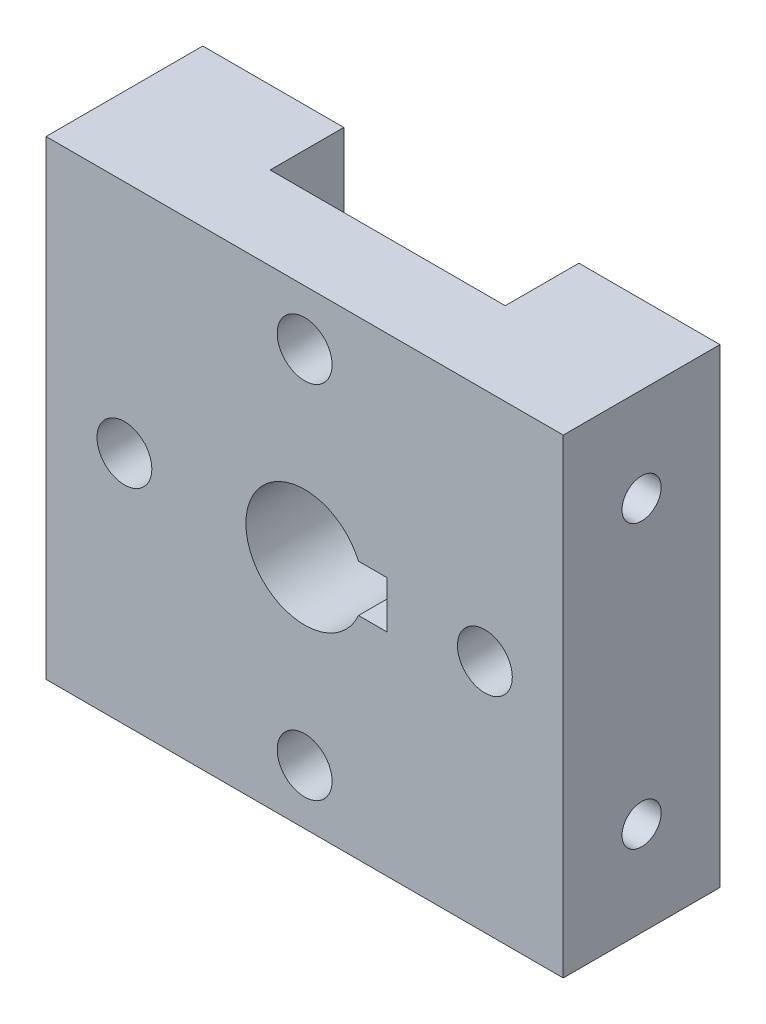
SolidWorks part; units mm, degrees
material "1.0037 (S235JR)"
ref_plane "Front Plane" through (0, 0, 0) normal (0, 0, 1) x (1, 0, 0)
ref_plane "Top Plane" through (0, 0, 0) normal (0, 1, 0) x (1, 0, 0)
ref_plane "Right Plane" through (0, 0, 0) normal (1, 0, 0) x (0, 0, -1)
sketch "Sketch1" plane through (0, 0, 0) normal (0, 0, 1) x (1, 0, 0)
  line L1 (33, 30) -> (-33, 30)
  line L2 (33, 30) -> (33, -30)
  line L3 (33, -30) -> (-33, -30)
  line L4 (-33, 30) -> (-33, -30)
  line L5 (33, 30) -> (-33, -30) construction
  line L6 (33, -30) -> (-33, 30) construction
  line L7 (4.5, -3) -> (10.5, -3)
  line L8 (4.5, -3) -> (4.5, 3)
  line L9 (4.5, 3) -> (10.5, 3)
  line L10 (10.5, -3) -> (10.5, 3)
  line L11 (4.5, -3) -> (10.5, 3) construction
  line L12 (4.5, 3) -> (10.5, -3) construction
  circle A0 centre (0, 0) radius 7.5
  point P0 (0, 0)
  point P8 (7.5, 0)
  dimension "D3" = 15
  dimension "D1" = 60
  dimension "D2" = 66
  dimension "D4" = 6
  dimension "D5" = 6
extrude "Boss-Extrude1" add sketch "Sketch1" along normal blind 20 contours L1 L4 L3 L2 A0 L9 L10 L7
sketch "Sketch2" plane through (0, 30, 0) normal (0, 1, 0) x (1, 0, 0)
  line L0 (33, 0) -> (-33, 0) construction
  line L1 (-15, 0) -> (15, 0)
  line L2 (-15, 0) -> (-15, -9.4)
  line L3 (-15, -9.4) -> (15, -9.4)
  line L4 (15, 0) -> (15, -9.4)
  line L5 (33, -20) -> (-33, -20) construction
  line L6 (-15, -9.4) -> (-33, -9.4) construction
  line L7 (-33, -20) -> (-33, 0) construction
  line L8 (15, -9.4) -> (33, -9.4) construction
  line L9 (33, -20) -> (33, 0) construction
  dimension "D1" = 10.6
  dimension "D2" = 30
extrude "Cut-Extrude1" cut sketch "Sketch2" against normal up to next
sketch "Sketch3" plane through (-33, 0, 0) normal (-1, 0, 0) x (0, 0, 1)
  line L0 (0, 30) -> (10, 30) construction
  line L1 (20, 30) -> (0, 30) construction
  line L2 (10, 30) -> (10, 18) construction
  line L3 (10, 18) -> (10, -18) construction
  line L4 (10, -18) -> (10, -30) construction
  line L5 (20, -30) -> (0, -30) construction
  point P0 (10, 18)
  point P1 (10, -18)
  dimension "D1" = 36
hole_wizard "M6 Tapped Hole1" positions "3DSketch2" profile "Sketch5" tap size "M6" standard "ISO"
sketch3d "3DSketch2"
  point P0 (-33, 18, 10)
  point P3 (-33, -18, 10)
sketch "Sketch5" plane through (-33, 18, 10) normal (0, 1, 0) x (0, 0, 1)
  line L0 (0, 0) -> (0, 29.5022)
  line L1 (0, 29.5022) -> (2.5, 28)
  line L2 (2.5, 28) -> (2.5, 0)
  line L5 (2.5, 0) -> (0, 0)
  line L10 (0, 29.5022) -> (-2.5, 28) construction
  line L11 (0, -6.35) -> (0, 107.95) construction
  dimension "Tap Drill Dia." = 5
  dimension "Tap Drill Depth" = 28
  dimension "Drill Angle" = 118
cosmetic thread "Hole Thread1" parameters "D1"=12, "D2"=6
cosmetic thread "Hole Thread2" parameters "D1"=12, "D2"=6
mirror "Mirror1" about plane through (0, 0, 0) normal (1, 0, 0) of "M6 Tapped Hole1"
cosmetic thread "Hole Thread3" parameters "D1"=12, "D2"=6
cosmetic thread "Hole Thread4" parameters "D1"=12, "D2"=6
sketch "Sketch7" plane through (0, 0, 20) normal (0, 0, 1) x (1, 0, 0)
  circle A1 centre (0, 0) radius 23 construction
  circle A2 centre (0, 23) radius 3.5
  circle A3 centre (23, 0) radius 3.5
  circle A4 centre (0, -23) radius 3.5
  circle A5 centre (-23, 0) radius 3.5
  dimension "D1" = 46
  dimension "D2" = 7
extrude "Cut-Extrude2" cut sketch "Sketch7" against normal through all
sketch "Sketch9" plane through (0, 0, 0) normal (0, 0, -1) x (-1, 0, 0)
  circle A0 centre (23, 0) radius 6
  circle A1 centre (-23, 0) radius 6
  dimension "D1" = 12
extrude "Cut-Extrude3" cut sketch "Sketch9" against normal blind 6
